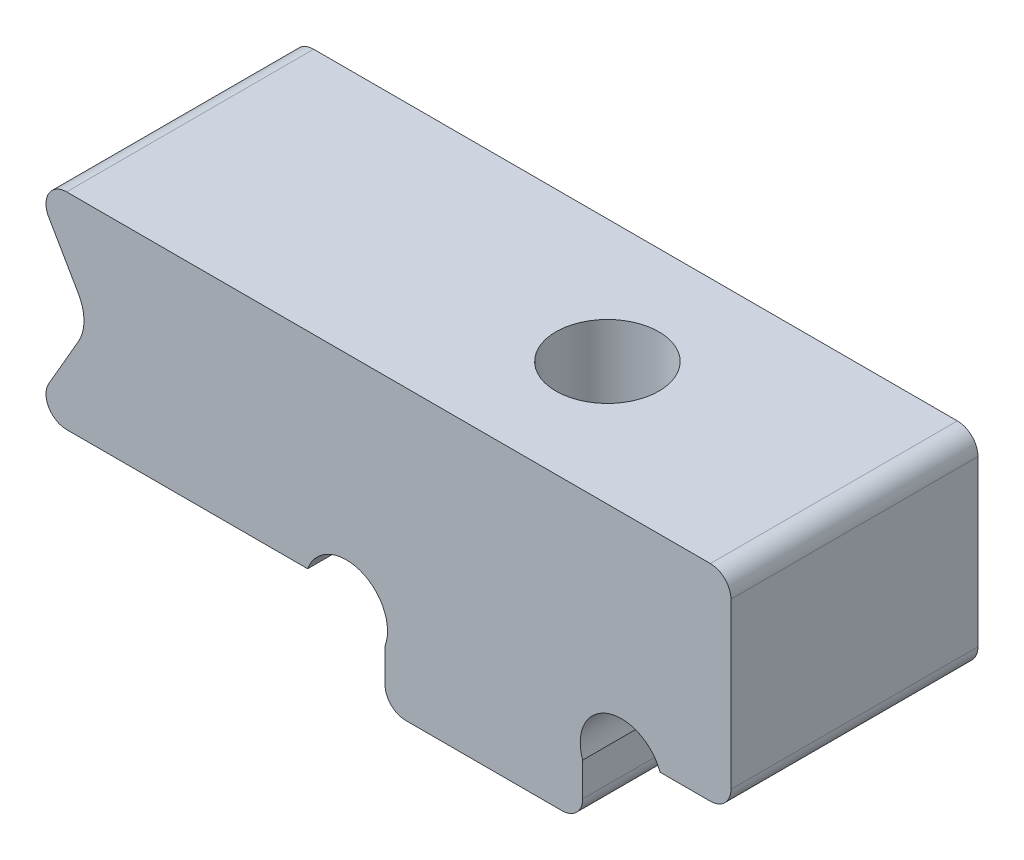
SolidWorks part; units mm, degrees
ref_plane "Plan de face" through (0, 0, 0) normal (0, 0, 1) x (1, 0, 0)
ref_plane "Plan de dessus" through (0, 0, 0) normal (0, 1, 0) x (1, 0, 0)
ref_plane "Plan de droite" through (0, 0, 0) normal (1, 0, 0) x (0, 0, -1)
sketch "Esquisse1" plane through (0, 0, 0) normal (0, 0, 1) x (1, 0, 0)
  line L0 (-6, 0) -> (-2.4, 0)
  line L1 (-2.4, -2) -> (2.4, -2)
  line L2 (-6, 0) -> (-6, 5)
  line L3 (-6, 5) -> (6, 5)
  line L4 (6, 0) -> (6, 5)
  line L5 (-6, 0) -> (6, 0) construction
  line L7 (-2.4, 0) -> (-2.4, -2)
  line L8 (6, 0) -> (2.4, 0)
  line L9 (2.4, 0) -> (2.4, -2)
  point P0 (0, 0)
  dimension "D1" = 12
  dimension "D2" = 4.8
  dimension "D3" = 5
  dimension "D4" = 2
extrude "Boss.-Extru.1" add sketch "Esquisse1" along normal mid plane 6
sketch "Esquisse2" plane through (0, 5, 0) normal (0, 1, 0) x (1, 0, 0)
  circle A0 centre (0, 0) radius 1.25
  dimension "D1" = 2.5
extrude "Enlèv. mat.-Extru.1" cut sketch "Esquisse2" against normal through all
sketch "Esquisse3" plane through (-6, 0, 0) normal (-1, 0, 0) x (0, 0, 1)
  line L1 (-3, 5) -> (3, 5)
  line L2 (-3, 5) -> (-3, 0)
  line L3 (-3, 0) -> (3, 0)
  line L4 (3, 5) -> (3, 0)
extrude "Boss.-Extru.2" add sketch "Esquisse3" along normal blind 5
sketch "Esquisse7" plane through (0, 0, 3) normal (0, 0, 1) x (1, 0, 0)
  line L0 (-11, 5) -> (-11, 0) construction
  line L1 (-11, 5) -> (-9.5566, 2.5)
  line L2 (-9.5566, 2.5) -> (-11, 0)
  line L3 (-11, 5) -> (-11, 0)
  line L4 (-11, 0) -> (-2.4, 0) construction
  point P6 (-11, 2.5)
  dimension "D1" = 120
extrude "Enlèv. mat.-Extru.3" cut sketch "Esquisse7" against normal through all
sketch3d "Esquisse3D1"
  line L0 (-9.5566, 2.5, -3) -> (-9.5566, 2.5, 3) construction
fillet "Congé4" radius 0.5 6 edges at (6, 5, 0) (6, 0, 0) (2.4, -2, 0) (-2.4, -2, 0) (-11, 5, 0) (-11, 0, 0)
fillet "Congé5" radius 1 1 edges at (-9.5566, 2.5, 0)
sketch "Esquisse8" plane through (0, 0, 0) normal (0, -1, 0) x (1, 0, 0)
  line L0 (2.4, 3) -> (2.4, -3) construction
  line L1 (-2.4, -1.25) -> (2.4, -1.25)
  line L2 (-2.4, -1.25) -> (-2.4, 1.25)
  line L3 (-2.4, 1.25) -> (2.4, 1.25)
  line L4 (2.4, -1.25) -> (2.4, 1.25)
  line L5 (-2.4, -1.25) -> (2.4, 1.25) construction
  line L6 (-2.4, 1.25) -> (2.4, -1.25) construction
  circle A0 centre (0, 0) radius 1.25 construction
  point P0 (0, 0)
sketch "Esquisse12" plane through (0, 0, -3) normal (0, 0, -1) x (-1, 0, 0)
  line L8 (-4.2794, 0) -> (-2.4, -0.684)
  line L11 (-2.4, 0) -> (-5.5, 0) construction
  line L12 (-2.4, -1.5) -> (-2.4, 0) construction
  line L13 (0, 3.85) -> (0, -3.85) construction
  line L14 (4.2794, 0) -> (2.4, -0.684)
  arc A2 (-4.2794, 0) -> (-2.4, -0.684) centre (-3.3397, -0.342) cw
  arc A3 (4.2794, 0) -> (2.4, -0.684) centre (3.3397, -0.342) ccw
  dimension "D2" = 70
  dimension "D3" = 2
extrude "Enlèv. mat.-Extru.5" cut sketch "Esquisse12" against normal through all
